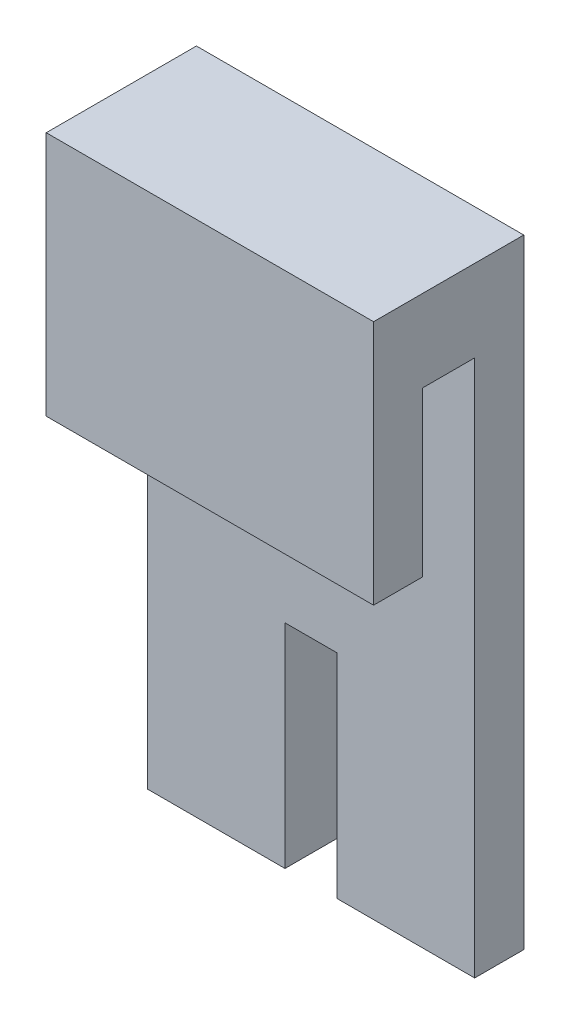
SolidWorks part; units mm, degrees
ref_plane "Front Plane" through (0, 0, 0) normal (0, 0, 1) x (1, 0, 0)
ref_plane "Top Plane" through (0, 0, 0) normal (0, 1, 0) x (1, 0, 0)
ref_plane "Right Plane" through (0, 0, 0) normal (1, 0, 0) x (0, 0, -1)
sketch "Sketch1" plane through (0, 0, 0) normal (1, 0, 0) x (0, 0, -1)
  line L0 (0, 0) -> (3, 0)
  line L1 (3, 0) -> (3, 10)
  line L2 (3, 10) -> (6.175, 10)
  line L3 (6.175, 10) -> (6.175, -22.812)
  line L4 (6.175, -22.812) -> (9.175, -22.812)
  line L5 (9.175, -22.812) -> (9.175, 15)
  line L6 (9.175, 15) -> (0, 15)
  line L7 (0, 15) -> (0, 0)
  dimension "D1" = 3
  dimension "D2" = 10
  dimension "D3" = 3.175
  dimension "D4" = 32.812
  dimension "D5" = 3
  dimension "D6" = 5
extrude "Boss-Extrude1" add sketch "Sketch1" along normal blind 20
sketch "Sketch2" plane through (0, 0, -9.175) normal (0, 0, -1) x (-1, 0, 0)
  line L0 (-11.5875, -22.812) -> (-11.5875, -9.812)
  line L1 (-20, -22.812) -> (0, -22.812) construction
  line L2 (-11.5875, -9.812) -> (-8.4125, -9.812)
  line L3 (-8.4125, -9.812) -> (-8.4125, -22.812)
  line L4 (-8.4125, -22.812) -> (-5.4125, -22.812)
  line L5 (-5.4125, -22.812) -> (-5.4125, -6.812)
  line L6 (-5.4125, -6.812) -> (-14.5875, -6.812)
  line L7 (-14.5875, -6.812) -> (-14.5875, -22.812)
  line L8 (-14.5875, -22.812) -> (-11.5875, -22.812)
  line L11 (-20, 15) -> (0, 15) construction
  point P8 (-10, -22.812)
  point P11 (-10, -9.812)
  dimension "D2" = 3
  dimension "D4" = 3
  dimension "D5" = 3.175
  dimension "D1" = 24.812
  dimension "D3" = 3
extrude "Boss-Extrude2" add sketch "Sketch2" along normal blind 5
sketch "Sketch3" plane through (0, 0, -9.175) normal (0, 0, -1) x (-1, 0, 0)
  line L0 (-11.5875, -9.812) -> (-11.5875, -22.812)
  line L1 (-11.5875, -22.812) -> (-8.4125, -22.812)
  line L2 (-8.4125, -22.812) -> (-8.4125, -9.812)
  line L3 (-8.4125, -9.812) -> (-11.5875, -9.812)
extrude "Cut-Extrude1" cut sketch "Sketch3" against normal up to surface (3 mm away) up to face at (10, -6.406, -6.175)
equation "\"bottomThickness\"= .220in"
equation "\"wallThickness\"= .125in"
equation "\"D3@Sketch1\"=\"wallThickness\""
equation "\"D5@Sketch2\"=\"wallThickness\""
